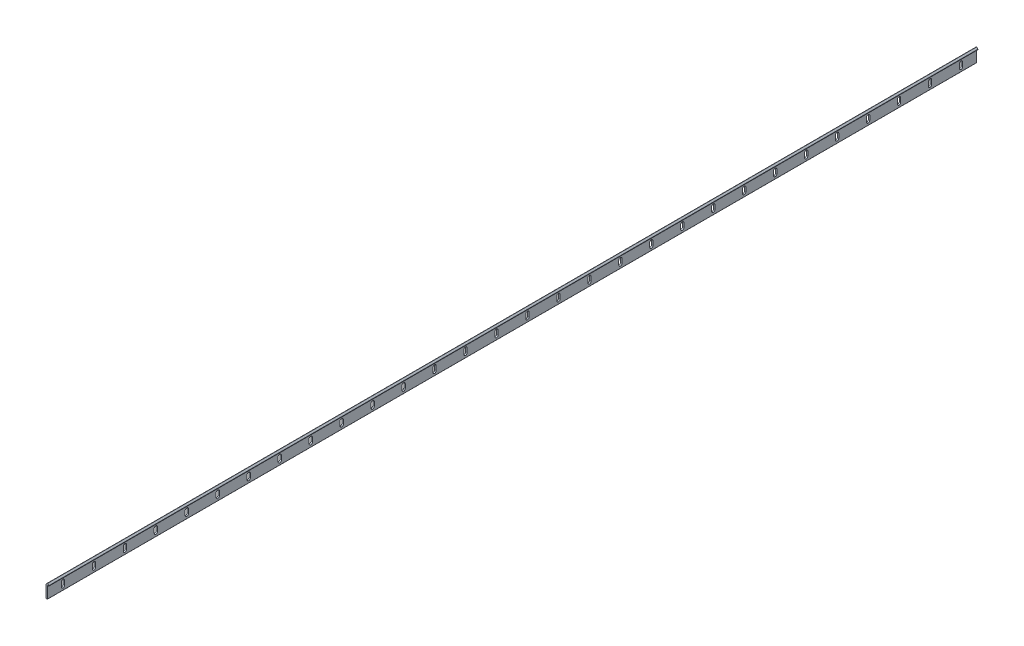
SolidWorks part; units mm, degrees
material "6061-T6 (SS)"
ref_plane "Front Plane" through (0, 0, 0) normal (0, 0, 1) x (1, 0, 0)
ref_plane "Top Plane" through (0, 0, 0) normal (0, 1, 0) x (1, 0, 0)
ref_plane "Right Plane" through (0, 0, 0) normal (1, 0, 0) x (0, 0, -1)
sketch "Sketch1" plane through (0, 0, 0) normal (0, 0, 1) x (1, 0, 0)
  line L0 (0, 0.3) -> (0, 20.125)
  line L1 (0.0879, 20.3371) -> (2.1629, 22.4121)
  line L2 (2.5871, 22.4121) -> (4.6621, 20.3371)
  line L3 (4.75, 20.125) -> (4.75, 19.85)
  line L4 (4.45, 19.55) -> (2.375, 19.55)
  line L5 (2.375, 19.55) -> (2.375, 0.3)
  line L6 (2.075, 0) -> (0.3, 0)
  arc A0 (4.75, 19.85) -> (4.45, 19.55) centre (4.45, 19.85) cw
  arc A1 (4.6621, 20.3371) -> (4.75, 20.125) centre (4.45, 20.125) cw
  arc A2 (0, 20.125) -> (0.0879, 20.3371) centre (0.3, 20.125) cw
  arc A3 (2.1629, 22.4121) -> (2.5871, 22.4121) centre (2.375, 22.2) cw
  arc A4 (0, 0.3) -> (0.3, 0) centre (0.3, 0.3) ccw
  arc A5 (2.375, 0.3) -> (2.075, 0) centre (2.075, 0.3) cw
  point P10 (4.75, 19.55)
  point P13 (4.75, 20.2493)
  point P16 (0, 20.2493)
  point P21 (0, 0)
  point P24 (2.375, 0)
  dimension "D4" = 0.3
  dimension "D6" = 0.3
  dimension "D1" = 2.375
  dimension "D2" = 19.55
  dimension "D3" = 2.375
  dimension "D5" = 22.5
extrude "Boss-Extrude1" add sketch "Sketch1" along normal blind 1500
sketch "Sketch2" plane through (2.375, 0, 0) normal (1, 0, 0) x (0, 0, -1)
  line L0 (-25, 12.7) -> (-25, 6) construction
  line L1 (-22.35, 12.7) -> (-22.35, 6)
  line L2 (-27.65, 12.7) -> (-27.65, 6)
  line L3 (0, 0.3) -> (0, 19.55) construction
  line L4 (-1500, 0) -> (0, 0) construction
  arc A0 (-22.35, 12.7) -> (-27.65, 12.7) centre (-25, 12.7) ccw
  arc A1 (-27.65, 6) -> (-22.35, 6) centre (-25, 6) ccw
  point P2 (-25, 9.35)
  dimension "D1" = 25
  dimension "D2" = 5.3
  dimension "D3" = 6.7
  dimension "D4" = 6
extrude "Cut-Extrude1" cut sketch "Sketch2" against normal through all
pattern_linear "LPattern1" count 30 spacing 50 along (0, 0, 1) of "Cut-Extrude1"
